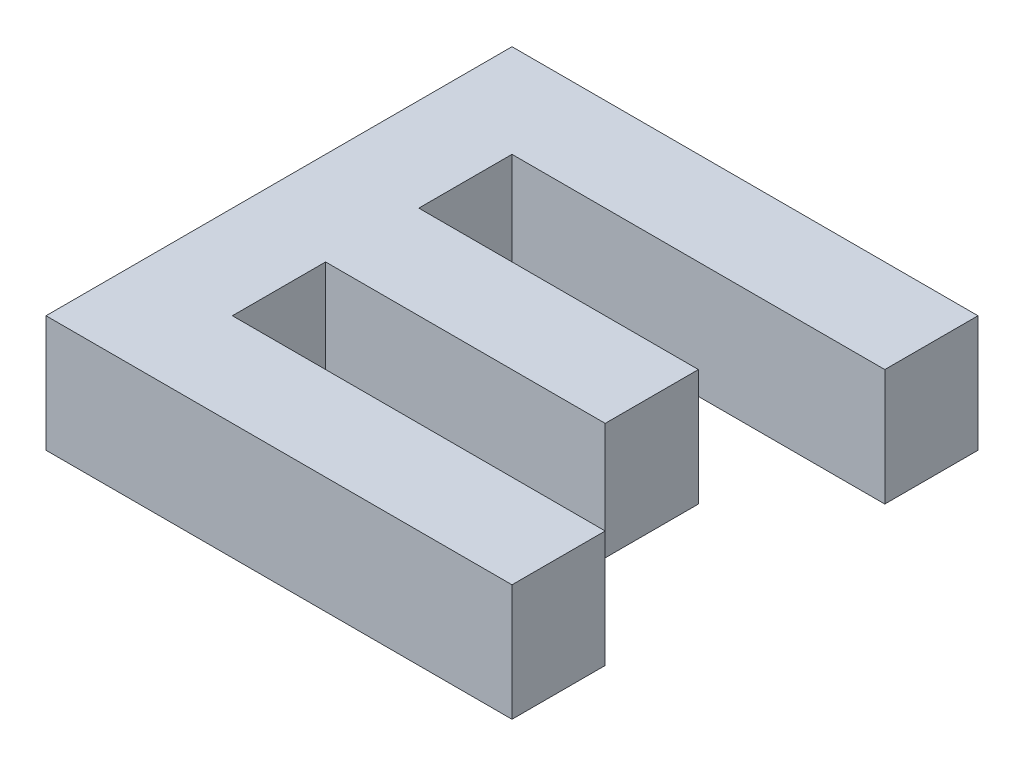
SolidWorks part; units mm, degrees
ref_plane "Front Plane" through (0, 0, 0) normal (0, 0, 1) x (1, 0, 0)
ref_plane "Top Plane" through (0, 0, 0) normal (0, 1, 0) x (1, 0, 0)
ref_plane "Right Plane" through (0, 0, 0) normal (1, 0, 0) x (0, 0, -1)
sketch "Sketch1" plane through (0, 0, 0) normal (0, 1, 0) x (1, 0, 0)
  line L0 (200, 0) -> (240, 0)
  line L1 (200, 0) -> (200, 40)
  line L2 (200, 40) -> (240, 40)
  line L3 (240, 40) -> (240, 32)
  line L4 (240, 32) -> (208, 32)
  line L5 (208, 32) -> (208, 24)
  line L6 (208, 24) -> (232, 24)
  line L7 (232, 24) -> (232, 16)
  line L8 (232, 16) -> (208, 16)
  line L9 (208, 16) -> (208, 8)
  line L10 (208, 8) -> (240, 8)
  line L11 (240, 8) -> (240, 0)
  point P1 (220, 24)
  dimension "D1" = 40
  dimension "D2" = 40
  dimension "D3" = 8
  dimension "D4" = 8
  dimension "D5" = 8
  dimension "D6" = 8
  dimension "D7" = 8
  dimension "D8" = 200
  dimension "D9" = 8
extrude "Boss-Extrude1" add sketch "Sketch1" along normal blind 10
